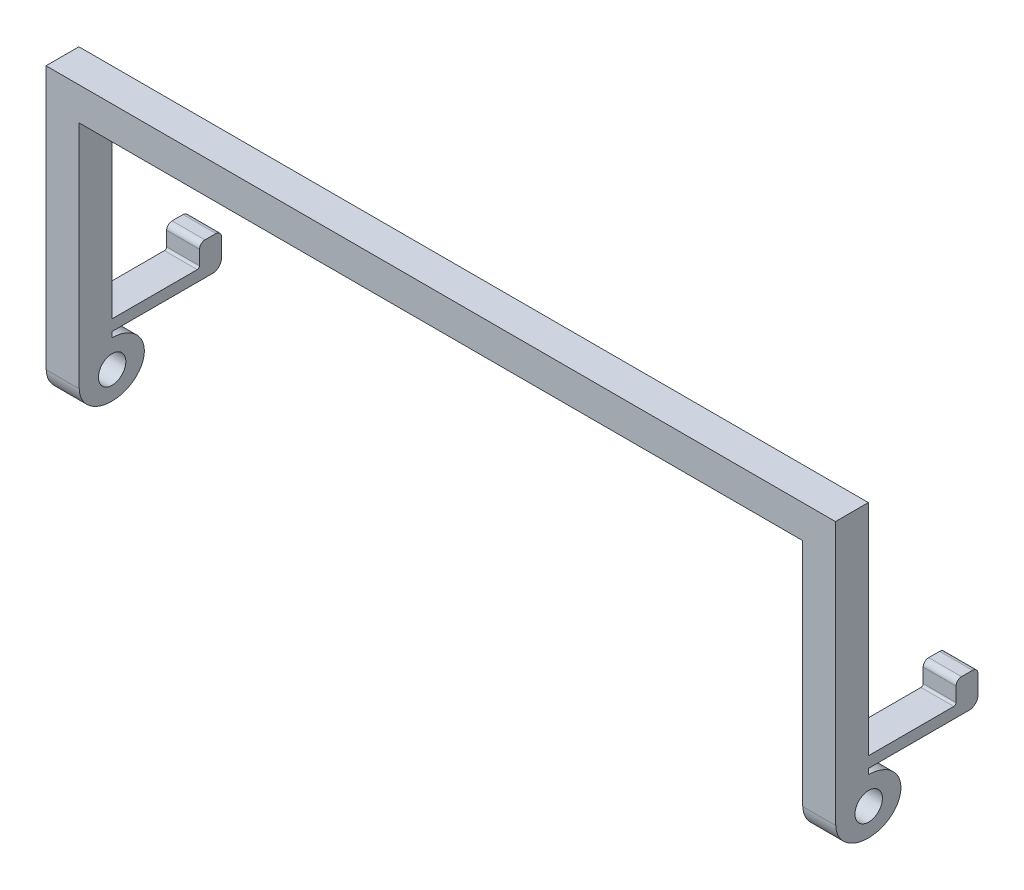
SolidWorks part; units mm, degrees
material "PTFE (general)"
ref_plane "Front Plane" through (0, 0, 0) normal (0, 0, 1) x (1, 0, 0)
ref_plane "Top Plane" through (0, 0, 0) normal (0, 1, 0) x (1, 0, 0)
ref_plane "Right Plane" through (0, 0, 0) normal (1, 0, 0) x (0, 0, -1)
sketch "Sketch1" plane through (0, 0, 0) normal (0, 0, 1) x (1, 0, 0)
  line L1 (0, 0) -> (36, 0)
  line L2 (0, 0) -> (0, 3)
  line L3 (0, 3) -> (36, 3)
  line L4 (36, 0) -> (36, 3)
  dimension "D1" = 36
  dimension "D2" = 3
extrude "Boss-Extrude1" add sketch "Sketch1" along normal blind 3
sketch "Sketch2" plane through (36, 0, 0) normal (1, 0, 0) x (0, 0, -1)
  line L0 (0, -17) -> (7.8, -17)
  line L1 (-3, 3) -> (0, 3)
  line L2 (-3, 3) -> (-3, -21)
  line L3 (-3, -21) -> (-2.9691, -21)
  line L4 (0, 3) -> (0, -17)
  line L5 (8, -16.8) -> (8, -15.5)
  line L6 (8.5, -15) -> (9.5, -15)
  line L7 (10, -15.5) -> (10, -17.2)
  line L8 (9.2, -18) -> (0, -18)
  line L9 (0, -18) -> (0, -18.5)
  line L10 (0, -21) -> (6.513, -21) construction
  line L11 (0, -21) -> (5.3712, -20.0529) construction
  line L12 (0, -21) -> (0, -26.2288) construction
  arc A0 (9.5, -15) -> (10, -15.5) centre (9.5, -15.5) cw
  arc A1 (8, -15.5) -> (8.5, -15) centre (8.5, -15.5) cw
  arc A2 (9.2, -18) -> (10, -17.2) centre (9.2, -17.2) ccw
  arc A3 (7.8, -17) -> (8, -16.8) centre (7.8, -16.8) ccw
  ellipse E0 centre (0, -21) end of major axis (2.9691, -21) minor radius 2.5 (-2.9691, -21) -> (0, -18.5) ccw
  point P13 (10, -15)
  point P16 (8, -15)
  point P19 (10, -18)
  point P22 (8, -17)
  dimension "D8" = 0.5
  dimension "D9" = 0.8
  dimension "D10" = 0.2
  dimension "D1" = 24
  dimension "D2" = 3
  dimension "D3" = 2
  dimension "D4" = 10
  dimension "D5" = 2
  dimension "D6" = 3
  dimension "D7" = 20
  dimension "D11" = 5
  dimension "D12" = 5.9691
  dimension "D13" = 10
extrude "Boss-Extrude2" add sketch "Sketch2" against normal blind 3
mirror "Mirror1" about plane through (0, 0, 3) normal (1, 0, 0) of "Boss-Extrude2", "Boss-Extrude1"
sketch "Sketch3" plane through (36, 0, 0) normal (1, 0, 0) x (0, 0, -1)
  line L0 (-3, 3) -> (0, 3) construction
  circle A1 centre (0.0309, -21) radius 1.25
  dimension "D1" = 2.5
  dimension "D2" = 3
  dimension "D3" = 24
extrude "Cut-Extrude1" cut sketch "Sketch3" against normal through all both and the other way through all
